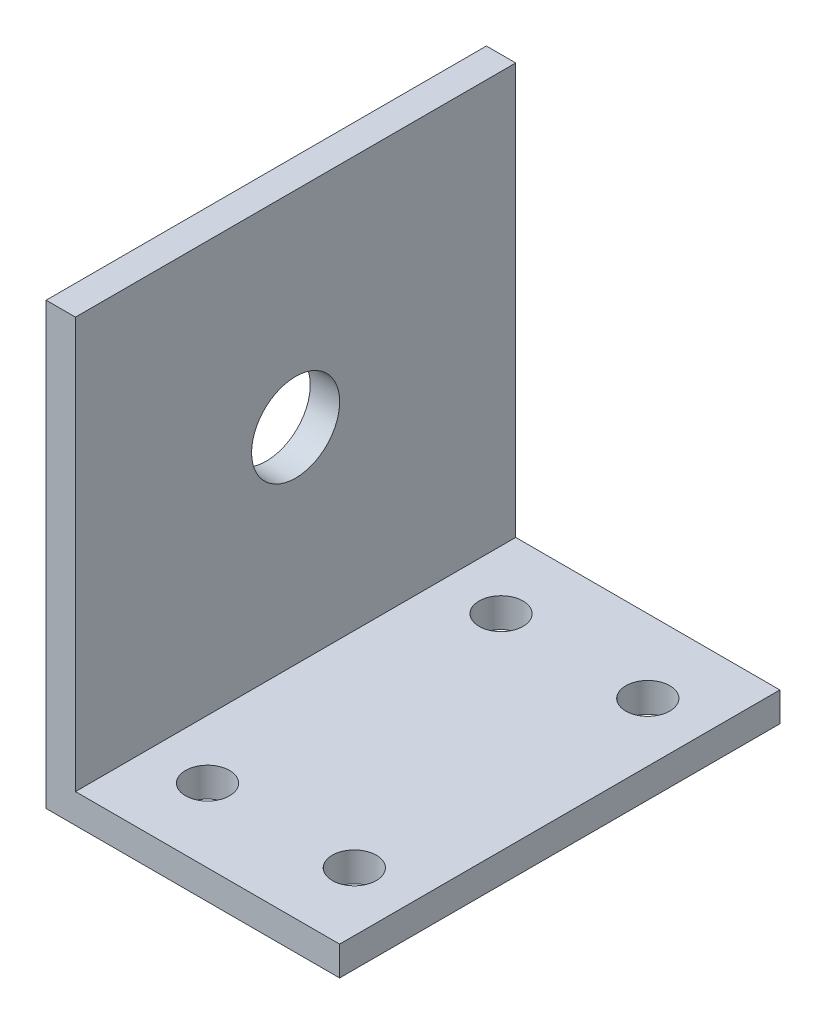
SolidWorks part; units mm, degrees
material "6063-O"
ref_plane "Front" through (0, 0, 0) normal (0, 0, 1) x (1, 0, 0)
ref_plane "Top" through (0, 0, 0) normal (0, 1, 0) x (1, 0, 0)
ref_plane "Right" through (0, 0, 0) normal (1, 0, 0) x (0, 0, -1)
sketch "草图1" plane through (0, 0, 0) normal (0, 0, 1) x (1, 0, 0)
  line L0 (0, 0) -> (0, 38)
  line L1 (0, 38) -> (3, 38)
  line L2 (3, 38) -> (3, 3)
  line L3 (3, 3) -> (38, 3)
  line L4 (38, 3) -> (38, 0)
  line L5 (38, 0) -> (0, 0)
  dimension "D1" = 38
  dimension "D2" = 3
  dimension "D3" = 35
  dimension "D4" = 35
extrude "凸台-拉伸1" add sketch "草图1" along normal blind 20
sketch "草图2" plane through (0, 0, 0) normal (-1, 0, 0) x (0, 0, 1)
  line L0 (20, 3) -> (20, 38) construction
  line L2 (20, 0) -> (0, 0) construction
  circle A0 centre (5, 16) radius 3
  dimension "D1" = 6
  dimension "D2" = 16
  dimension "D3" = 15
extrude "切除-拉伸1" cut sketch "草图2" against normal through all
sketch "草图4" plane through (0, 38, 0) normal (0, 1, 0) x (1, 0, 0)
  line L0 (3, -20) -> (0, -20) construction
  line L1 (3, -20) -> (0, -20)
  line L2 (3, -20) -> (3, 0)
  line L3 (3, 0) -> (0, 0)
  line L4 (0, -20) -> (0, 0)
extrude "切除-拉伸3" cut sketch "草图4" against normal blind 8
sketch "草图5" plane through (0, 3, 0) normal (0, 1, 0) x (1, 0, 0)
  line L0 (38, -20) -> (3, -20) construction
  line L1 (3, -20) -> (38, -20)
  line L2 (3, -20) -> (3, 0)
  line L3 (3, 0) -> (38, 0)
  line L4 (38, -20) -> (38, 0)
  line L5 (38, 0) -> (3, 0) construction
extrude "切除-拉伸4" cut sketch "草图5" against normal blind 1
sketch "草图6" plane through (3, 0, 0) normal (1, 0, 0) x (0, 0, -1)
  line L0 (-20, 2) -> (-20, 30) construction
  line L1 (-20, 30) -> (0, 30)
  line L2 (-20, 30) -> (-20, 2)
  line L3 (-20, 2) -> (0, 2)
  line L4 (0, 30) -> (0, 2)
  line L5 (-20, 30) -> (0, 30) construction
  line L6 (0, 2) -> (0, 30) construction
extrude "切除-拉伸5" cut sketch "草图6" against normal blind 1
sketch "草图8" plane through (38, 0, 0) normal (1, 0, 0) x (0, 0, -1)
  line L0 (-20, 0) -> (0, 0) construction
  line L1 (-20, 2) -> (0, 2)
  line L2 (-20, 2) -> (-20, 0)
  line L3 (-20, 0) -> (0, 0)
  line L4 (0, 2) -> (0, 0)
extrude "切除-拉伸6" cut sketch "草图8" against normal blind 18
sketch "草图9" plane through (0, 0, 0) normal (0, 0, -1) x (-1, 0, 0)
  line L0 (0, 0) -> (-20, 0) construction
  line L1 (0, 30) -> (-2, 30)
  line L2 (0, 30) -> (0, 0)
  line L3 (0, 0) -> (-2, 0)
  line L4 (-2, 30) -> (-2, 0)
  line L5 (-2, 2) -> (-2, 30) construction
  line L6 (-2, 0) -> (-20, 0)
  line L7 (-2, 0) -> (-2, 2)
  line L8 (-2, 2) -> (-20, 2)
  line L9 (-20, 0) -> (-20, 2)
  line M1 (-2, 2) -> (-20, 2)
  line M2 (-20, 2) -> (-20, 0)
  line M3 (-20, 0) -> (0, 0)
  dimension "D1" = 0
extrude "凸台-拉伸2" add sketch "草图9" along normal blind 10 contours L4 L8 M1 M2 M3
sketch "草图10" plane through (0, 2, 0) normal (0, 1, 0) x (1, 0, 0)
  line L0 (20, 10) -> (20, -20) construction
  line L1 (2, -20) -> (20, -20) construction
  line L2 (2, 10) -> (20, 10) construction
  line L3 (2, -20) -> (2, 10) construction
  circle A0 centre (16, -15) radius 1.5
  circle A1 centre (16, 5) radius 1.5
  circle A2 centre (6, -15) radius 1.5
  circle A3 centre (6, 5) radius 1.5
  dimension "D7" = 3
  dimension "D8" = 3
  dimension "D9" = 3
  dimension "D10" = 3
  dimension "D12" = 4
  dimension "D1" = 4
  dimension "D2" = 4
  dimension "D3" = 5
  dimension "D4" = 5
  dimension "D5" = 5
  dimension "D6" = 5
  dimension "D11" = 4
extrude "切除-拉伸7" cut sketch "草图10" against normal blind 10
